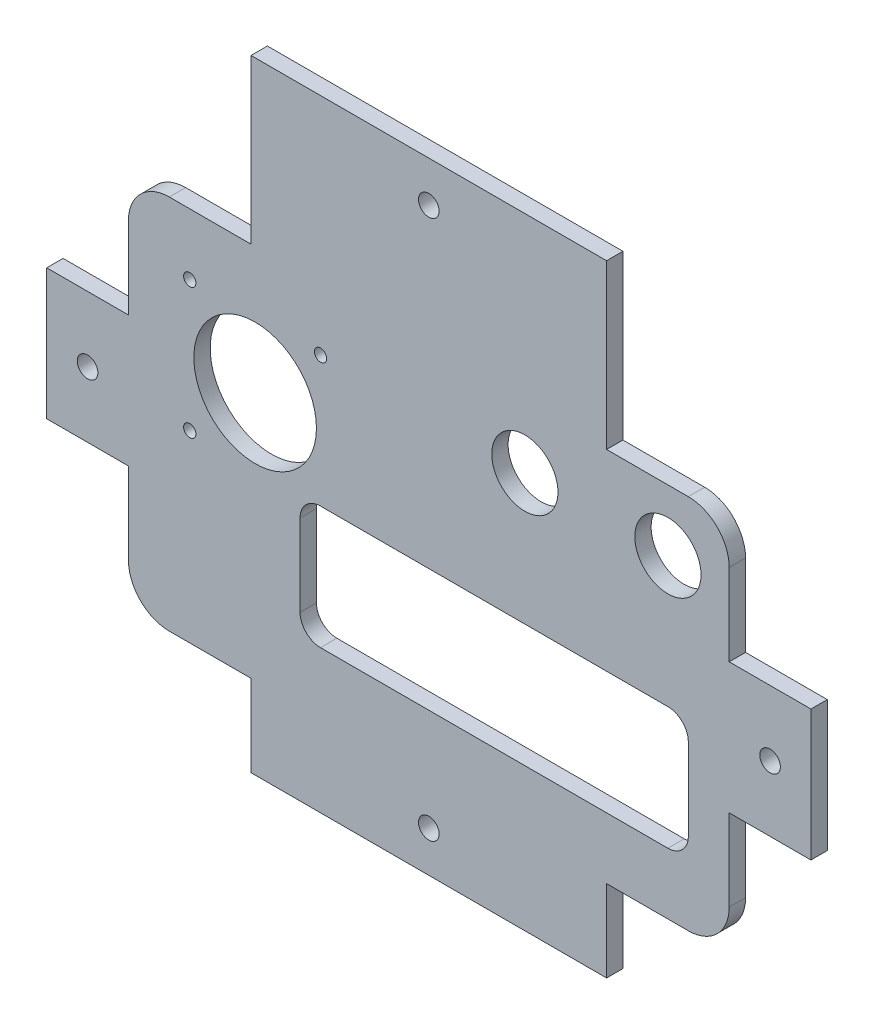
SolidWorks part; units mm, degrees
ref_plane "Front Plane" through (0, 0, 0) normal (0, 0, 1) x (1, 0, 0)
ref_plane "Top Plane" through (0, 0, 0) normal (0, 1, 0) x (1, 0, 0)
ref_plane "Right Plane" through (0, 0, 0) normal (1, 0, 0) x (0, 0, -1)
sketch "Model" plane through (0, 0, 0) normal (0, 0, 1) x (1, 0, 0)
  line L0 (58.5, -1) -> (-26.5, -1)
  line L1 (63.5, -26) -> (63.5, -6)
  line L2 (-26.5, -31) -> (58.5, -31)
  line L3 (-31.5, -6) -> (-31.5, -26)
  line L4 (-93.5, -16) -> (-73.5, -16)
  line L5 (-73.5, -16) -> (-73.5, -36)
  line L6 (-63.5, -46) -> (-43.5, -46)
  line L7 (-43.5, -46) -> (-43.5, -66)
  line L8 (-43.5, -66) -> (43.5, -66)
  line L9 (43.5, -66) -> (43.5, -46)
  line L10 (43.5, -46) -> (63.5, -46)
  line L11 (73.5, -36) -> (73.5, -16)
  line L12 (73.5, -16) -> (93.5, -16)
  line L13 (93.5, -16) -> (93.5, 16)
  line L14 (93.5, 16) -> (73.5, 16)
  line L15 (73.5, 16) -> (73.5, 36)
  line L16 (63.5, 46) -> (43.5, 46)
  line L17 (43.5, 46) -> (43.5, 86)
  line L18 (43.5, 86) -> (-43.5, 86)
  line L19 (-43.5, 86) -> (-43.5, 46)
  line L20 (-43.5, 46) -> (-63.5, 46)
  line L21 (-73.5, 36) -> (-73.5, 16)
  line L22 (-73.5, 16) -> (-93.5, 16)
  line L23 (-93.5, 16) -> (-93.5, -16)
  line L24 (-42.5, 15) -> (-26.5, 31) construction
  line L25 (-42.5, 15) -> (-58.5, 31) construction
  line L26 (-42.5, 15) -> (-58.5, -1) construction
  line L27 (23.5, 31) -> (58.5, 31) construction
  line L28 (-83.5, 0) -> (-93.5, 0) construction
  line L29 (83.5, 0) -> (93.5, 0) construction
  line L30 (0, -56) -> (0, -66) construction
  line L31 (0, 76) -> (0, 86) construction
  line L32 (0, 76) -> (0, 0) construction
  line L33 (0, 0) -> (-83.5, 0) construction
  arc A0 (63.5, -6) -> (58.5, -1) centre (58.5, -6) ccw
  arc A1 (58.5, -31) -> (63.5, -26) centre (58.5, -26) ccw
  arc A2 (-31.5, -26) -> (-26.5, -31) centre (-26.5, -26) ccw
  arc A3 (-26.5, -1) -> (-31.5, -6) centre (-26.5, -6) ccw
  circle A4 centre (23.5, 31) radius 8.1
  circle A5 centre (-26.5, 31) radius 1.5
  circle A6 centre (-58.5, 31) radius 1.5
  circle A7 centre (83.5, 0) radius 2.525
  circle A8 centre (0, 76) radius 2.525
  arc A9 (-73.5, -36) -> (-63.5, -46) centre (-63.5, -36) ccw
  arc A10 (63.5, -46) -> (73.5, -36) centre (63.5, -36) ccw
  arc A11 (73.5, 36) -> (63.5, 46) centre (63.5, 36) ccw
  arc A12 (-63.5, 46) -> (-73.5, 36) centre (-63.5, 36) ccw
  circle A13 centre (-83.5, 0) radius 2.525
  circle A14 centre (0, -56) radius 2.525
  circle A15 centre (-58.5, -1) radius 1.5
  circle A16 centre (58.5, 31) radius 8.1
  circle A17 centre (-42.5, 15) radius 15
  dimension "D3" = 5
  dimension "D4" = 30
  dimension "D5" = 3
  dimension "D6" = 11
  dimension "D7" = 16
  dimension "D8" = 16
  dimension "D9" = 16
  dimension "D10" = 35
  dimension "D11" = 16.2
  dimension "D15" = 10
  dimension "D23" = 5.05
  dimension "D26" = 15
  dimension "D27" = 15
  dimension "D1" = 95
  dimension "D2" = 30
  dimension "D12" = 32
  dimension "D13" = 20
  dimension "D14" = 20
  dimension "D16" = 20
  dimension "D17" = 87
  dimension "D18" = 10
  dimension "D19" = 10
  dimension "D20" = 10
  dimension "D21" = 10
  dimension "D22" = 20
  dimension "D24" = 42
  dimension "D25" = 35
  dimension "D28" = 40
extrude "Boss-Extrude1" add sketch "Model" along normal blind 4
